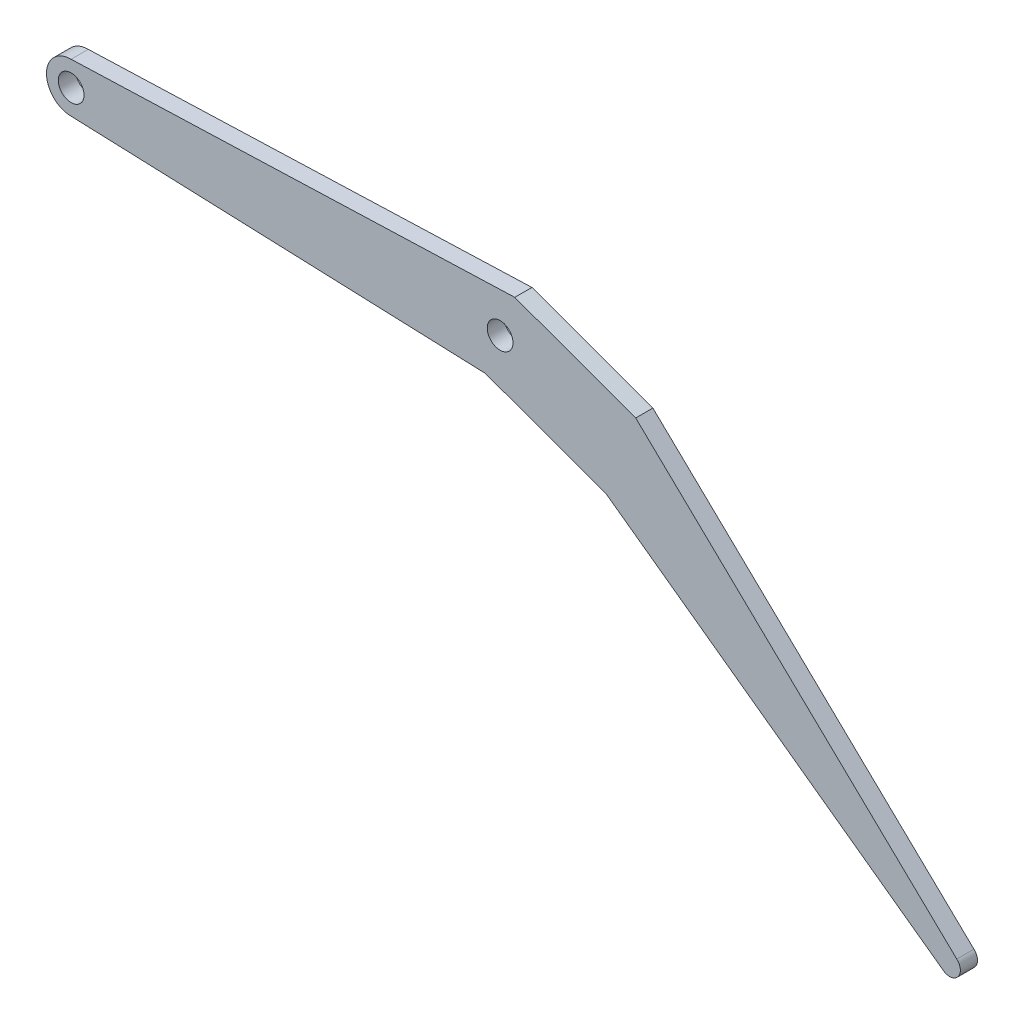
SolidWorks part; units mm, degrees
ref_plane "Front Plane" through (0, 0, 0) normal (0, 0, 1) x (1, 0, 0)
ref_plane "Top Plane" through (0, 0, 0) normal (0, 1, 0) x (1, 0, 0)
ref_plane "Right Plane" through (0, 0, 0) normal (1, 0, 0) x (0, 0, -1)
sketch "Sketch1" plane through (0, 0, 0) normal (0, 0, 1) x (1, 0, 0)
  line L0 (0, 0) -> (100, 0) construction
  line L1 (100, 0) -> (128.1908, -10.2606) construction
  line L2 (128.1908, -10.2606) -> (204.7952, -74.5394) construction
  line L3 (96.5798, -9.3969) -> (124.7706, -19.6575)
  line L4 (103.4202, 9.3969) -> (131.611, -0.8637)
  line L5 (103.4202, 9.3969) -> (-0.0052, 5.75)
  line L6 (0.0409, -5.7499) -> (96.5798, -9.3969)
  line L7 (131.611, -0.8637) -> (206.4615, -72.6757)
  line L8 (203.1289, -76.4031) -> (124.7706, -19.6575)
  circle A0 centre (0, 0) radius 3
  circle A1 centre (100, 0) radius 3
  arc A2 (-0.0052, 5.75) -> (0.0409, -5.7499) centre (0, 0) ccw
  arc A3 (206.4615, -72.6757) -> (203.1289, -76.4031) centre (204.7952, -74.5394) cw
  dimension "D8" = 6
  dimension "D9" = 11.5
  dimension "D10" = 5
  dimension "D1" = 100
  dimension "D2" = 100
  dimension "D3" = 30
  dimension "D4" = 160
  dimension "D5" = 160
  dimension "D6" = 10
  dimension "D7" = 10
extrude "Extrude1" add sketch "Sketch1" along normal blind 4
